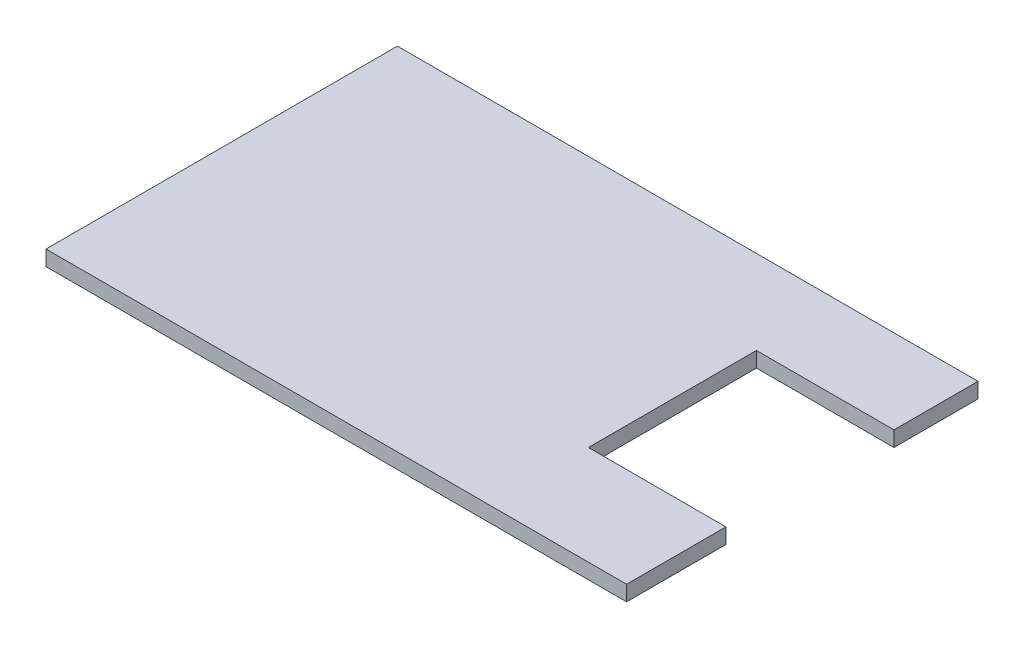
SolidWorks part; units mm, degrees
ref_plane "Front Plane" through (0, 0, 0) normal (0, 0, 1) x (1, 0, 0)
ref_plane "Top Plane" through (0, 0, 0) normal (0, 1, 0) x (1, 0, 0)
ref_plane "Right Plane" through (0, 0, 0) normal (1, 0, 0) x (0, 0, -1)
sketch "Sketch1" plane through (0, 0, 0) normal (0, 1, 0) x (1, 0, 0)
  line L0 (76, 35) -> (76, 46)
  line L1 (0, 0) -> (76, 0)
  line L2 (0, 0) -> (0, 46)
  line L3 (0, 46) -> (76, 46)
  line L4 (76, 0) -> (76, 13)
  line L5 (76, 35) -> (58, 35)
  line L7 (76, 13) -> (58, 13)
  line L8 (58, 35) -> (58, 13)
  dimension "D1" = 76
  dimension "D2" = 46
  dimension "D3" = 18
  dimension "D4" = 22
  dimension "D5" = 13
extrude "Boss-Extrude1" add sketch "Sketch1" along normal blind 2
